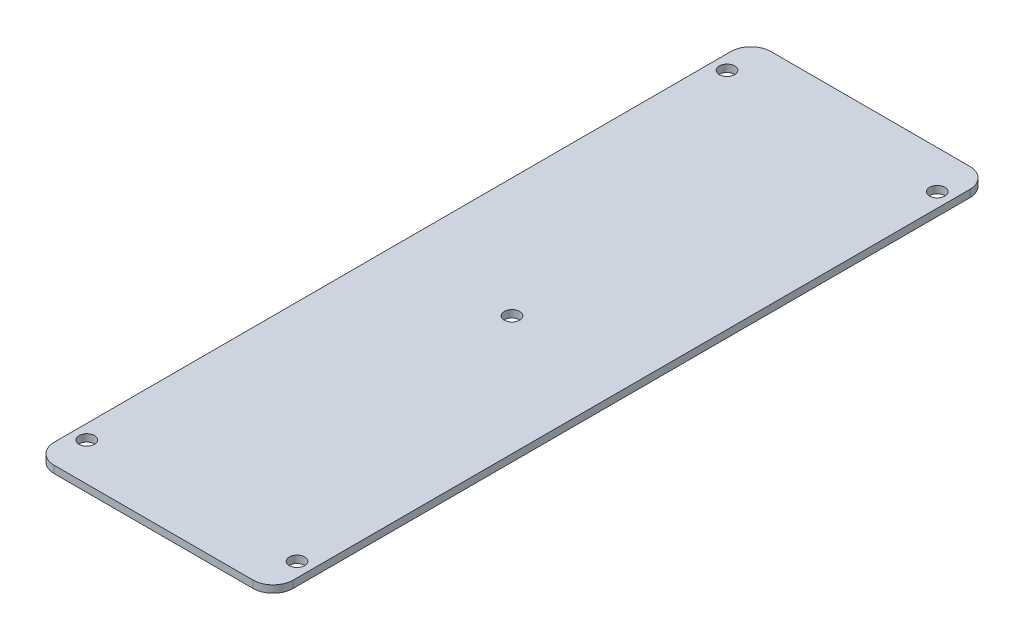
SolidWorks part; units mm, degrees
ref_plane "Front Plane" through (0, 0, 0) normal (0, 0, 1) x (1, 0, 0)
ref_plane "Top Plane" through (0, 0, 0) normal (0, 1, 0) x (1, 0, 0)
ref_plane "Right Plane" through (0, 0, 0) normal (1, 0, 0) x (0, 0, -1)
sketch "Sketch1" plane through (0, 0, 0) normal (0, 1, 0) x (1, 0, 0)
  line L1 (0, 0) -> (50, 0)
  line L2 (0, 0) -> (0, -150)
  line L3 (0, -150) -> (50, -150)
  line L4 (50, 0) -> (50, -150)
  dimension "D1" = 50
  dimension "D2" = 150
extrude "Boss-Extrude1" add sketch "Sketch1" along normal blind 1.524
sketch "Sketch2" plane through (0, 1.524, 0) normal (0, 1, 0) x (1, 0, 0)
  line L0 (50, 0) -> (0, 0) construction
  line L1 (50, -150) -> (50, 0) construction
  circle A0 centre (47, -8) radius 1.6
  dimension "D1" = 3.2
  dimension "D2" = 8
  dimension "D3" = 3
extrude "Cut-Extrude1" cut sketch "Sketch2" against normal up to surface (1.524 mm away) up to face at (25, 0, 75)
pattern_linear "LPattern1" count 2 spacing 44 along (-1, 0, 0) count 2 spacing 134 along (0, 0, 1) of "Cut-Extrude1"
fillet "Fillet1" radius 4.191 4 edges at (50, 0.762, 150) (0, 0.762, 150) (0, 0.762, 0) (50, 0.762, 0)
sketch "Sketch3" plane through (0, 1.524, 0) normal (0, 1, 0) x (1, 0, 0)
  line L0 (25, -150) -> (25, -8) construction
  line L1 (4.191, -150) -> (45.809, -150) construction
  line L2 (3, -142) -> (47, -142) construction
  line L3 (47, -8) -> (3, -8) construction
  circle A0 centre (25, -75) radius 1.6
  point P14 (25, -8)
  dimension "D1" = 3.2
  dimension "D2" = 67
extrude "Cut-Extrude2" cut sketch "Sketch3" against normal up to surface (1.524 mm away) up to face at (3, 0, 9.6)
